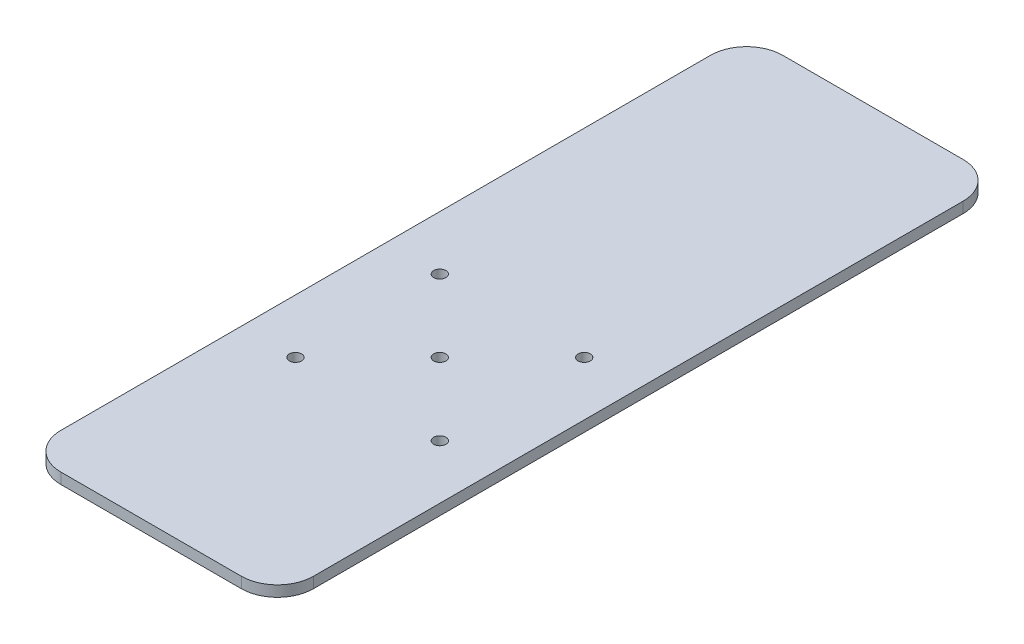
SolidWorks part; units mm, degrees
ref_plane "Alzado" through (0, 0, 0) normal (0, 0, 1) x (1, 0, 0)
ref_plane "Planta" through (0, 0, 0) normal (0, 1, 0) x (1, 0, 0)
ref_plane "Vista lateral" through (0, 0, 0) normal (1, 0, 0) x (0, 0, -1)
sketch "Croquis1" plane through (0, 0, 0) normal (0, 1, 0) x (1, 0, 0)
  line L1 (-25, -100) -> (25, -100)
  line L2 (-35, -90) -> (-35, 90)
  line L3 (-25, 100) -> (25, 100)
  line L4 (35, -90) -> (35, 90)
  line L5 (-35, -100) -> (35, 100) construction
  line L6 (-35, 100) -> (35, -100) construction
  arc A0 (-25, -100) -> (-35, -90) centre (-25, -90) cw
  arc A1 (25, -100) -> (35, -90) centre (25, -90) ccw
  arc A2 (25, 100) -> (35, 90) centre (25, 90) cw
  arc A3 (-35, 90) -> (-25, 100) centre (-25, 90) cw
  point P0 (0, 0)
  dimension "D3" = 10
  dimension "D1" = 200
  dimension "D2" = 70
extrude "Saliente-Extruir1" add sketch "Croquis1" along normal blind 3
hole_wizard "Taladro de margen para M31" positions "Croquis2" profile "Croquis3" hole size "M3" standard "ISO" end condition through all
sketch "Croquis2" plane through (0, 3, 0) normal (0, 1, 0) x (1, 0, 0)
  line L2 (0, -1000) -> (0, 49000) construction
  line L3 (-1000, -20) -> (49000, -20) construction
  point P0 (-20, 0)
  point P35 (-20, -40)
  point P36 (20, -40)
  point P37 (20, 0)
  point P38 (0, -20)
  dimension "D1" = 20
  dimension "D2" = 40
  dimension "D3" = 40
sketch "Croquis3" plane through (-20, 3, 0) normal (1, 0, 0) x (0, 0, 1)
  line L0 (0, 0) -> (0, 3)
  line L1 (0, 3) -> (1.7, 3)
  line L2 (1.7, 3) -> (1.7, 0)
  line L5 (1.7, 0) -> (0, 0)
  line L11 (0, -6.35) -> (0, 107.95) construction
  dimension "Diámetro de taladro hasta el siguiente" = 3.4
  dimension "Profundidad de taladro hasta el siguiente" = 3
